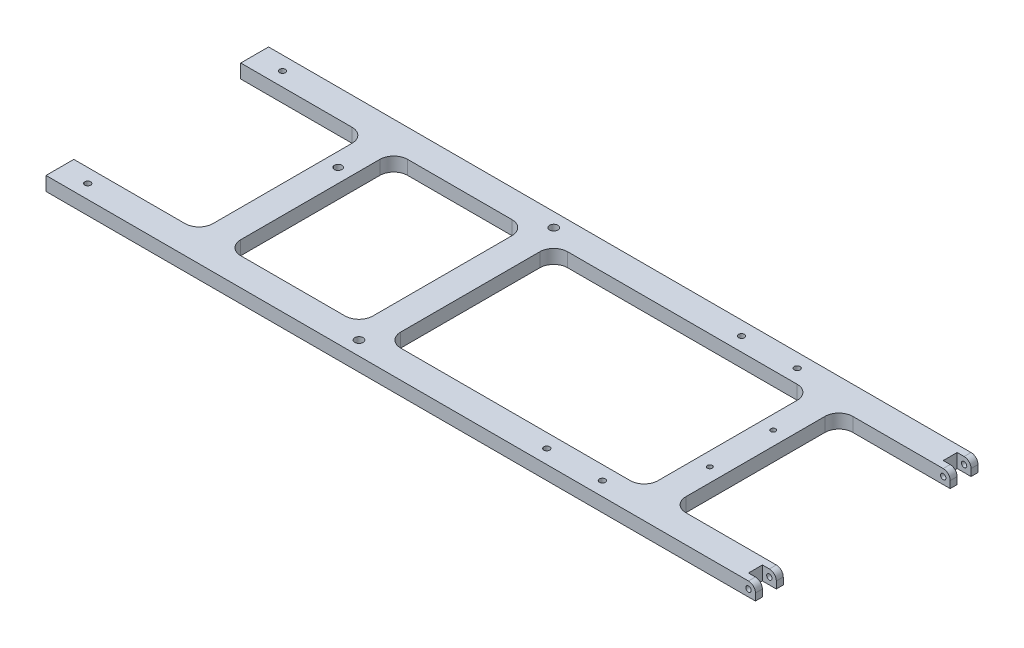
SolidWorks part; units mm, degrees
material "6061 Alloy"
ref_plane "Front Plane" through (0, 0, 0) normal (0, 0, 1) x (1, 0, 0)
ref_plane "Top Plane" through (0, 0, 0) normal (0, 1, 0) x (1, 0, 0)
ref_plane "Right Plane" through (0, 0, 0) normal (1, 0, 0) x (0, 0, -1)
sketch "Sketch1" plane through (0, 0, 0) normal (0, 1, 0) x (1, 0, 0)
  line L0 (-161.925, 0) -> (161.925, 0) construction
  line L1 (-161.925, 50.8) -> (161.925, 50.8)
  line L2 (-161.925, 50.8) -> (-161.925, -50.8)
  line L3 (-161.925, -50.8) -> (161.925, -50.8)
  line L4 (161.925, 50.8) -> (161.925, -50.8)
  line L6 (0, 50.8) -> (0, -50.8) construction
  dimension "D1" = 323.85
  dimension "D2" = 101.6
extrude "Extrude1" add sketch "Sketch1" along normal blind 6.35
sketch "Sketch2" plane through (0, 6.35, 0) normal (0, 1, 0) x (-1, 0, 0)
  line L0 (161.925, -50.8) -> (161.925, 50.8) construction
  line L1 (161.925, -38.1) -> (104.775, -38.1)
  line L2 (161.925, -38.1) -> (161.925, 38.1)
  line L3 (161.925, 38.1) -> (104.775, 38.1)
  line L4 (104.775, -38.1) -> (104.775, 38.1)
  line L5 (-161.925, -50.8) -> (161.925, -50.8) construction
  dimension "D1" = 76.2
  dimension "D2" = 57.15
  dimension "D3" = 12.7
extrude "Cut-Extrude1" cut sketch "Sketch2" against normal blind 6.35
sketch "Sketch3" plane through (0, 6.35, 0) normal (0, 1, 0) x (-1, 0, 0)
  line L0 (104.775, 38.1) -> (104.775, -38.1) construction
  line L1 (92.075, -38.1) -> (31.75, -38.1)
  line L2 (92.075, -38.1) -> (92.075, 38.1)
  line L3 (92.075, 38.1) -> (31.75, 38.1)
  line L4 (31.75, -38.1) -> (31.75, 38.1)
  line L5 (104.775, -38.1) -> (161.925, -38.1) construction
  line L6 (161.925, 38.1) -> (104.775, 38.1) construction
  line L7 (-161.925, 50.8) -> (-161.925, -50.8) construction
  line L8 (-161.925, -38.1) -> (-111.125, -38.1)
  line L9 (-161.925, -38.1) -> (-161.925, 38.1)
  line L10 (-161.925, 38.1) -> (-111.125, 38.1)
  line L11 (-111.125, -38.1) -> (-111.125, 38.1)
  line L13 (19.05, -38.1) -> (-98.425, -38.1)
  line L14 (19.05, -38.1) -> (19.05, 38.1)
  line L15 (19.05, 38.1) -> (-98.425, 38.1)
  line L16 (-98.425, -38.1) -> (-98.425, 38.1)
  dimension "D1" = 60.325
  dimension "D2" = 12.7
  dimension "D3" = 12.7
  dimension "D4" = 12.7
  dimension "D5" = 50.8
extrude "Cut-Extrude2" cut sketch "Sketch3" against normal blind 6.35
sketch "Sketch4" plane through (0, 6.35, 0) normal (0, 1, 0) x (-1, 0, 0)
  line L0 (-161.925, -38.1) -> (-161.925, -50.8) construction
  line L1 (-161.925, -47.625) -> (-155.575, -47.625)
  line L2 (-161.925, -47.625) -> (-161.925, -41.275)
  line L3 (-161.925, -41.275) -> (-155.575, -41.275)
  line L4 (-155.575, -47.625) -> (-155.575, -41.275)
  line L5 (-161.925, 50.8) -> (-161.925, 38.1) construction
  line L6 (-161.925, 41.275) -> (-155.575, 41.275)
  line L7 (-161.925, 41.275) -> (-161.925, 47.625)
  line L8 (-161.925, 47.625) -> (-155.575, 47.625)
  line L9 (-155.575, 41.275) -> (-155.575, 47.625)
  line L10 (-161.925, -50.8) -> (161.925, -50.8) construction
  line L11 (-111.125, 38.1) -> (-161.925, 38.1) construction
  dimension "D1" = 6.35
  dimension "D2" = 3.175
  dimension "D3" = 6.35
  dimension "D4" = 3.175
  dimension "D5" = 6.35
extrude "Cut-Extrude3" cut sketch "Sketch4" against normal blind 6.35
hole_wizard "#2 Clearance Hole1" positions "3DSketch1" profile "Sketch6" hole size "#2" standard "Ansi Inch" end condition through all
sketch3d "3DSketch1"
  line L0 (161.925, 6.35, 50.8) -> (161.925, 0, 50.8) construction
  line L1 (-161.925, 6.35, 50.8) -> (161.925, 6.35, 50.8) construction
  point P0 (158.75, 3.175, 50.8)
  dimension "D1" = 3.175
  dimension "D2" = 3.175
sketch "Sketch6" plane through (158.75, 3.175, 50.8) normal (1, 0, 0) x (0, -1, 0)
  line L0 (0, 0) -> (0, 101.6)
  line L1 (0, 101.6) -> (1.2192, 101.6)
  line L2 (1.2192, 101.6) -> (1.2192, 0)
  line L5 (1.2192, 0) -> (0, 0)
  line L11 (0, -6.35) -> (0, 107.95) construction
  dimension "Thru Hole Dia." = 2.4384
  dimension "Thru Hole Depth" = 101.6
fillet "Fillet1" radius 3.175 4 edges at (161.925, 6.35, -49.2125) (161.925, 6.35, -39.6875) (161.925, 6.35, 49.2125) (161.925, 6.35, 39.6875)
hole_wizard "Tap Drill for #8 Tap1" positions "3DSketch2" profile "Sketch8" hole size "#8-32" standard "Ansi Inch"
sketch3d "3DSketch2"
  line L0 (-92.075, 6.35, -38.1) -> (-92.075, 6.35, 38.1) construction
  line L1 (-31.75, 6.35, -38.1) -> (-92.075, 6.35, -38.1) construction
  point P0 (-98.425, 6.35, -19.05)
  dimension "D1" = 6.35
  dimension "D2" = 19.05
sketch "Sketch8" plane through (-98.425, 6.35, -19.05) normal (1, 0, 0) x (0, 0, 1)
  line L0 (0, 0) -> (0, 13.7378)
  line L1 (0, 13.7378) -> (1.7272, 12.7)
  line L2 (1.7272, 12.7) -> (1.7272, 0)
  line L5 (1.7272, 0) -> (0, 0)
  line L10 (0, 13.7378) -> (-1.7272, 12.7) construction
  line L11 (0, -6.35) -> (0, 107.95) construction
  dimension "Hole Dia." = 3.4544
  dimension "Hole Depth" = 12.7
  dimension "Drill Angle" = 118
hole_wizard "#6 Clearance Hole1" positions "3DSketch3" profile "Sketch9" hole size "#6" standard "Ansi Inch"
sketch3d "3DSketch3"
  line L0 (-31.75, 6.35, 38.1) -> (-31.75, 6.35, -38.1) construction
  line L1 (158.75, 6.35, -50.8) -> (-161.925, 6.35, -50.8) construction
  line L2 (-161.925, 6.35, 50.8) -> (158.75, 6.35, 50.8) construction
  point P0 (-25.4, 6.35, -44.45)
  point P2 (-25.4, 6.35, 44.45)
  dimension "D1" = 6.35
  dimension "D2" = 6.35
  dimension "D3" = 6.35
  dimension "D4" = 6.35
sketch "Sketch9" plane through (-25.4, 6.35, -44.45) normal (1, 0, 0) x (0, 0, 1)
  line L0 (0, 0) -> (0, 13.8408)
  line L1 (0, 13.8408) -> (1.8986, 12.7)
  line L2 (1.8986, 12.7) -> (1.8986, 0)
  line L5 (1.8986, 0) -> (0, 0)
  line L10 (0, 13.8408) -> (-1.8987, 12.7) construction
  line L11 (0, -6.35) -> (0, 107.95) construction
  dimension "Hole Dia." = 3.7973
  dimension "Hole Depth" = 12.7
  dimension "Drill Angle" = 118
hole_wizard "Tap Drill for #6 Tap1" positions "3DSketch4" profile "Sketch10" hole size "#6-32" standard "Ansi Inch"
sketch3d "3DSketch4"
  line L0 (-161.925, 6.35, -50.8) -> (-161.925, 6.35, -38.1) construction
  line L1 (-161.925, 6.35, 38.1) -> (-161.925, 6.35, 50.8) construction
  line L2 (-161.925, 6.35, 38.1) -> (-104.775, 6.35, 38.1) construction
  line L3 (-104.775, 6.35, -38.1) -> (-161.925, 6.35, -38.1) construction
  point P0 (-149.225, 6.35, -44.45)
  point P2 (-149.225, 6.35, 44.45)
  dimension "D1" = 12.7
  dimension "D2" = 12.7
  dimension "D3" = 6.35
  dimension "D4" = 6.35
sketch "Sketch10" plane through (-149.225, 6.35, -44.45) normal (1, 0, 0) x (0, 0, 1)
  line L0 (0, 0) -> (0, 13.5127)
  line L1 (0, 13.5127) -> (1.3525, 12.7)
  line L2 (1.3525, 12.7) -> (1.3525, 0)
  line L5 (1.3525, 0) -> (0, 0)
  line L10 (0, 13.5127) -> (-1.3526, 12.7) construction
  line L11 (0, -6.35) -> (0, 107.95) construction
  dimension "Hole Dia." = 2.7051
  dimension "Hole Depth" = 12.7
  dimension "Drill Angle" = 118
fillet "Fillet2" radius 6.35 8 edges at (111.125, 3.175, 38.1) (111.125, 3.175, -38.1) (-104.775, 3.175, -38.1) (-104.775, 3.175, 38.1) (-31.75, 3.175, 38.1) (-92.075, 3.175, 38.1) (-31.75, 3.175, -38.1) (-92.075, 3.175, -38.1)
fillet "Fillet3" radius 6.35 4 edges at (98.425, 3.175, 38.1) (98.425, 3.175, -38.1) (-19.05, 3.175, 38.1) (-19.05, 3.175, -38.1)
hole_wizard "Tap Drill for #6 Tap2" positions "3DSketch5" profile "Sketch11" hole size "#6-32" standard "Ansi Inch"
sketch3d "3DSketch5"
  line L0 (161.925, 0, -50.8) -> (-161.925, 0, -50.8) construction
  line L1 (-161.925, 0, 50.8) -> (161.925, 0, 50.8) construction
  line L2 (98.425, 0, 31.75) -> (98.425, 0, -31.75) construction
  point P0 (60.325, 0, 44.45)
  point P2 (85.725, 0, 44.45)
  point P4 (60.325, 0, -44.45)
  point P6 (85.725, 0, -44.45)
  dimension "D1" = 6.35
  dimension "D2" = 6.35
  dimension "D3" = 38.1
  dimension "D4" = 25.4
sketch "Sketch11" plane through (60.325, 0, 44.45) normal (1, 0, 0) x (0, 0, -1)
  line L0 (0, 0) -> (0, 102.4127)
  line L1 (0, 102.4127) -> (1.3525, 101.6)
  line L2 (1.3525, 101.6) -> (1.3525, 0)
  line L5 (1.3525, 0) -> (0, 0)
  line L10 (0, 102.4127) -> (-1.3526, 101.6) construction
  line L11 (0, -6.35) -> (0, 107.95) construction
  dimension "Hole Dia." = 2.7051
  dimension "Hole Depth" = 101.6
  dimension "Drill Angle" = 118
hole_wizard "Tap Drill for #4 Tap1" positions "3DSketch6" profile "Sketch12" hole size "#4-40" standard "Ansi Inch" end condition through all
sketch3d "3DSketch6"
  line L0 (98.425, 6.35, 31.75) -> (98.425, 6.35, -31.75) construction
  line L1 (98.425, 6.35, 0) -> (111.125, 6.35, 0) construction
  line L2 (111.125, 6.35, -31.75) -> (111.125, 6.35, 31.75) construction
  point P0 (104.775, 6.35, 14.478)
  point P2 (104.775, 6.35, -14.478)
  dimension "D1" = 6.35
  dimension "D2" = 28.956
  dimension "D3" = 6.35
  dimension "D4" = 14.478
sketch "Sketch12" plane through (104.775, 6.35, 14.478) normal (1, 0, 0) x (0, 0, 1)
  line L0 (0, 0) -> (0, 6.35)
  line L1 (0, 6.35) -> (1.1303, 6.35)
  line L2 (1.1303, 6.35) -> (1.1303, 0)
  line L5 (1.1303, 0) -> (0, 0)
  line L11 (0, -6.35) -> (0, 107.95) construction
  dimension "Thru Hole Dia." = 2.2606
  dimension "Thru Hole Depth" = 6.35
